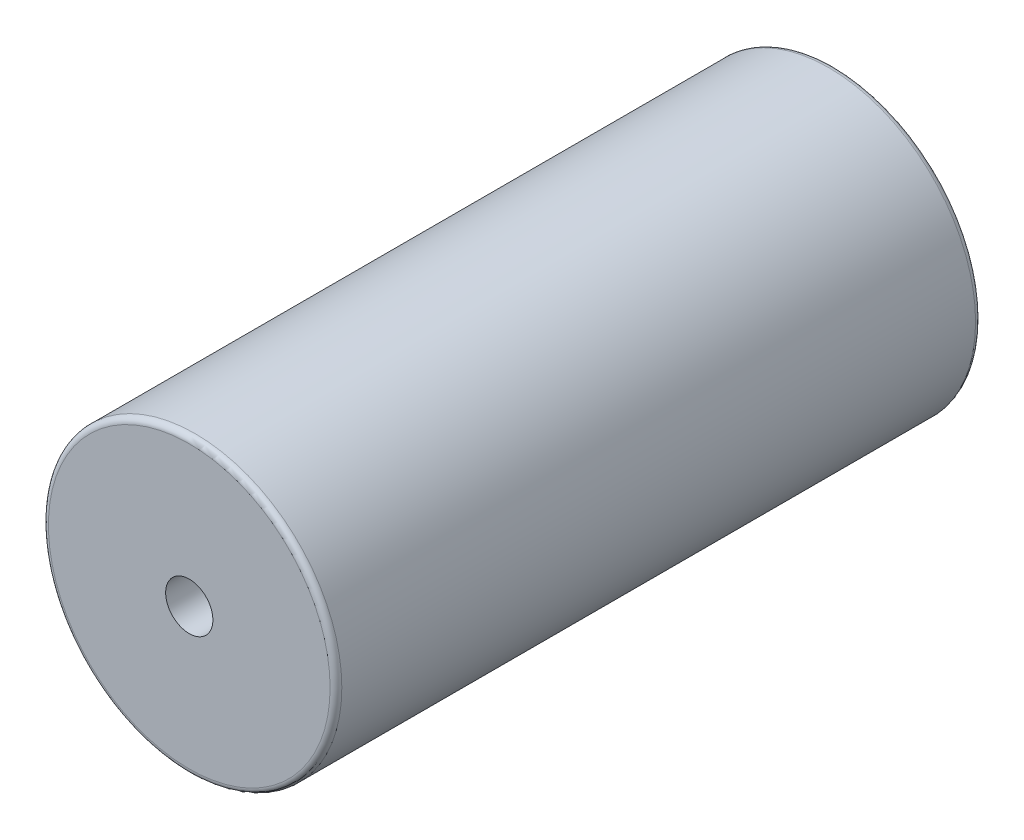
SolidWorks part; units mm, degrees
ref_plane "Ebene vorne" through (0, 0, 0) normal (0, 0, 1) x (1, 0, 0)
ref_plane "Ebene oben" through (0, 0, 0) normal (0, 1, 0) x (1, 0, 0)
ref_plane "Ebene rechts" through (0, 0, 0) normal (1, 0, 0) x (0, 0, -1)
sketch "Skizze1" plane through (0, 0, 0) normal (0, 0, 1) x (1, 0, 0)
  circle A0 centre (0, 0) radius 4.025
  circle A1 centre (0, 0) radius 25
  dimension "D1" = 8.05
  dimension "D2" = 50
extrude "Aufsatz-Linear austragen1" add sketch "Skizze1" along normal blind 110
fillet "Verrundung1" radius 1 2 edges at (25, 0, 0) (25, 0, 110)
